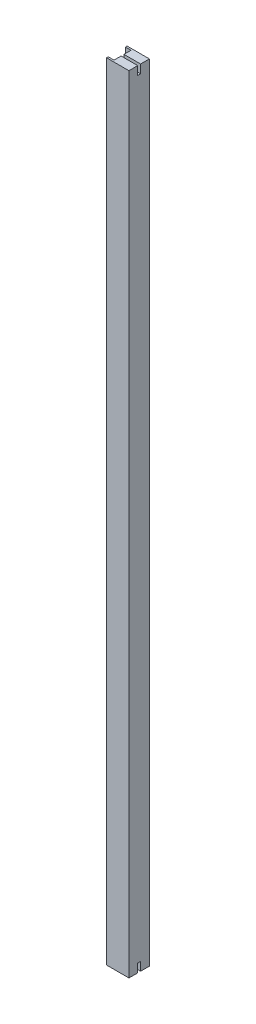
SolidWorks part; units mm, degrees
ref_plane "Спереди" through (0, 0, 0) normal (0, 0, 1) x (1, 0, 0)
ref_plane "Сверху" through (0, 0, 0) normal (0, 1, 0) x (1, 0, 0)
ref_plane "Справа" through (0, 0, 0) normal (1, 0, 0) x (0, 0, -1)
sketch "Эскиз1" plane through (0, 0, 0) normal (0, 1, 0) x (1, 0, 0)
  line L1 (10, 2.5) -> (10, 15)
  line L2 (10, 15) -> (0, 15)
  line L3 (0, 15) -> (0, 18)
  line L4 (0, 18) -> (39.2552, 18)
  line L5 (39.2552, 18) -> (39.2552, -18)
  line L7 (10, 2.5) -> (0, 2.5)
  line L8 (0, 2.5) -> (0, -2.5)
  line L9 (-20.2057, 0) -> (49.5465, 0) construction
  line L10 (10, -2.5) -> (0, -2.5)
  line L11 (0, -18) -> (39.2552, -18)
  line L12 (0, -15) -> (0, -18)
  line L13 (10, -15) -> (0, -15)
  line L14 (10, -2.5) -> (10, -15)
  point P12 (0, 0)
  point P14 (39.2552, 0)
  point P17 (0, 0)
  point P18 (0, 0)
  point P19 (0, 0)
extrude "Бобышка-Вытянуть1" add sketch "Эскиз1" along normal blind 1383.55
sketch "Эскиз3" plane through (39.2552, 0, 0) normal (1, 0, 0) x (0, 0, -1)
  line L0 (2.5, 0) -> (-2.5, 0)
  line L1 (-18, 0) -> (18, 0) construction
  line L2 (-2.5, 0) -> (-2.5, 15)
  line L3 (-2.5, 15) -> (2.5, 15)
  line L4 (0, -5.4444) -> (0, 1435.7196) construction
  line L5 (2.5, 0) -> (2.5, 15)
  line L6 (44.6402, 691.775) -> (-39.1393, 691.775) construction
  line L7 (2.5, 1383.55) -> (2.5, 1368.55)
  line L8 (-2.5, 1368.55) -> (2.5, 1368.55)
  line L9 (-2.5, 1383.55) -> (-2.5, 1368.55)
  line L10 (2.5, 1383.55) -> (-2.5, 1383.55)
  line L11 (18, 1383.55) -> (18, 0) construction
  point P10 (0, 15)
  point P11 (0, 0)
  point P19 (18, 691.775)
extrude "Вырез-Вытянуть4" cut sketch "Эскиз3" against normal through all
